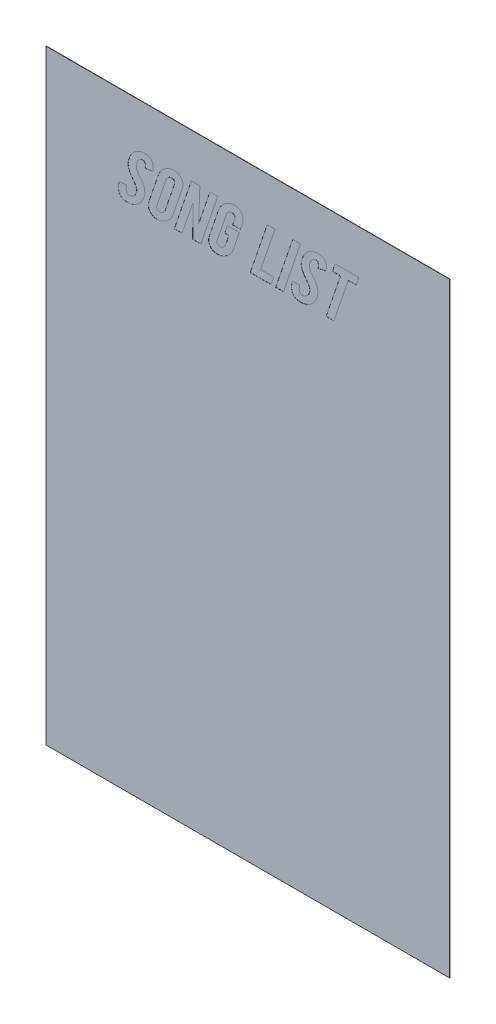
SolidWorks part; units mm, degrees
ref_plane "Front Plane" through (0, 0, 0) normal (0, 0, 1) x (1, 0, 0)
ref_plane "Top Plane" through (0, 0, 0) normal (0, 1, 0) x (1, 0, 0)
ref_plane "Right Plane" through (0, 0, 0) normal (1, 0, 0) x (0, 0, -1)
sketch "Sketch1" plane through (0, 0, 0) normal (0, 0, 1) x (1, 0, 0)
  line L1 (0, 0) -> (101.6, 0)
  line L2 (0, 0) -> (0, 152.4)
  line L3 (0, 152.4) -> (101.6, 152.4)
  line L4 (101.6, 0) -> (101.6, 152.4)
  dimension "D1" = 152.4
  dimension "D2" = 101.6
extrude "Boss-Extrude1" add sketch "Sketch1" along normal blind 0.0762
sketch "Sketch2" plane through (0, 0, 0.0762) normal (0, 0, 1) x (1, 0, 0)
  text T0 "Song   List" font "Bebas" height in points 40
  point P1 (8.0841, 115.5506)
  point P5 (31.4365, 235.2784)
  point P6 (12.1614, 234.089)
extrude "Cut-Extrude1" cut sketch "Sketch2" against normal blind 0.0254
